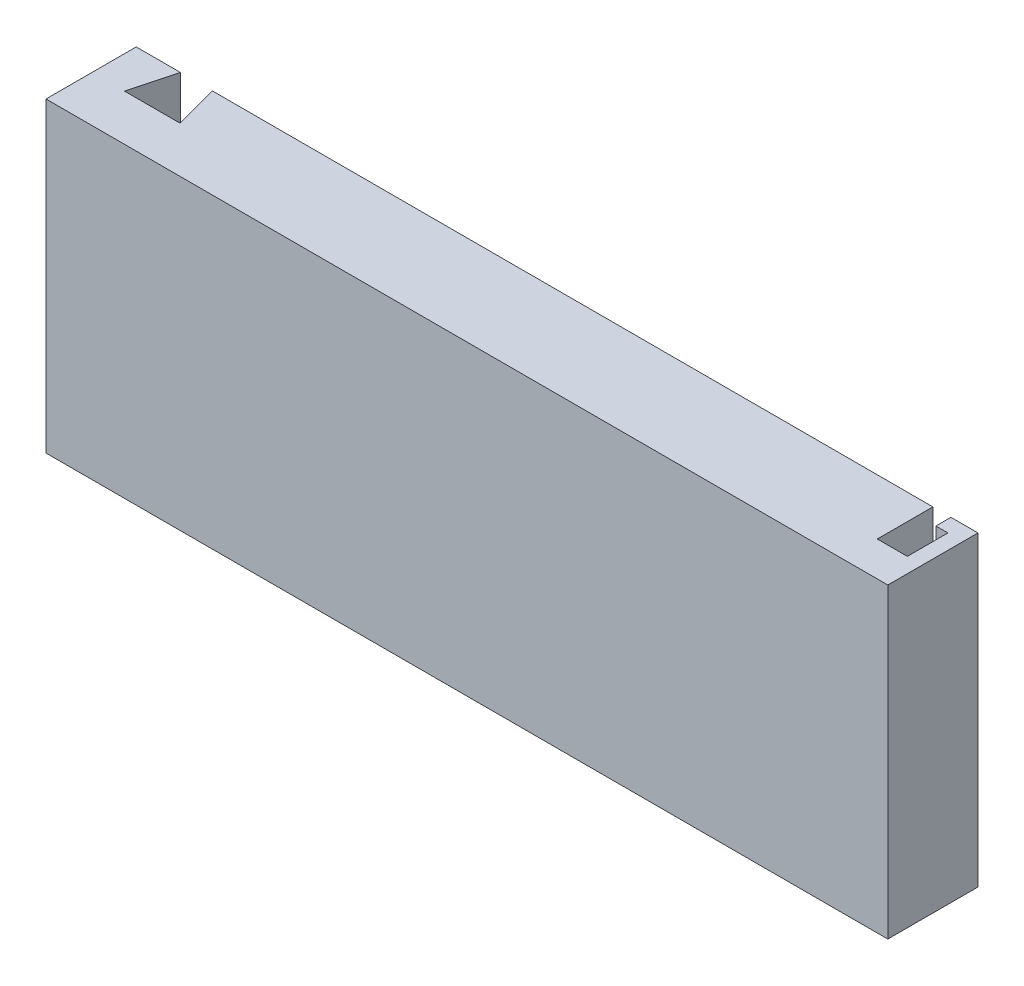
SolidWorks part; units mm, degrees
ref_plane "Front Plane" through (0, 0, 0) normal (0, 0, 1) x (1, 0, 0)
ref_plane "Top Plane" through (0, 0, 0) normal (0, 1, 0) x (1, 0, 0)
ref_plane "Right Plane" through (0, 0, 0) normal (1, 0, 0) x (0, 0, -1)
sketch "Sketch1" plane through (0, 0, 0) normal (0, 0, 1) x (1, 0, 0)
  line L1 (-60.9366, 28.6127) -> (79.0634, 28.6127)
  line L2 (-60.9366, 28.6127) -> (-60.9366, -22.3873)
  line L3 (-60.9366, -22.3873) -> (79.0634, -22.3873)
  line L4 (79.0634, 28.6127) -> (79.0634, -22.3873)
  dimension "D1" = 51
  dimension "D2" = 140
extrude "Boss-Extrude1" add sketch "Sketch1" along normal blind 15
sketch "Sketch2" plane through (0, 28.6127, 0) normal (0, 1, 0) x (1, 0, 0)
  line L0 (79.0634, 0) -> (74.5634, 0)
  line L6 (79.0634, 0) -> (-60.9366, 0) construction
  line L7 (74.5634, 0) -> (71.5634, 0)
  line L8 (71.5634, 0) -> (71.5634, -2.5)
  line L9 (71.5634, -2.5) -> (71.5634, -9.25)
  line L10 (71.5634, -9.25) -> (76.5634, -9.25)
  line L11 (74.5634, 0) -> (74.5634, -2.5)
  line L12 (74.5634, -2.5) -> (76.5634, -2.5)
  line L13 (76.5634, -2.5) -> (76.5634, -9.25)
  line M13 (79.0634, 0) -> (-60.9366, 0)
  dimension "D1" = 4.5
  dimension "D2" = 3
  dimension "D3" = 2.5
  dimension "D4" = 6.75
  dimension "D5" = 5
extrude "Cut-Extrude1" cut sketch "Sketch2" against normal through all contours L13 L12 L11 L8 L9 L10 M13
sketch "Sketch3" plane through (0, 28.6127, 0) normal (0, 1, 0) x (1, 0, 0)
  line L0 (-60.9366, 0) -> (-53.5866, 0)
  line L2 (71.5634, 0) -> (-60.9366, 0) construction
  line L3 (-53.5866, 0) -> (-55.5536, -7.341)
  line L4 (-55.5536, -7.341) -> (-46.3196, -7.341)
  line L5 (-46.3196, -7.341) -> (-48.2866, 0)
  dimension "D1" = 7.35
  dimension "D2" = 105
  dimension "D3" = 105
  dimension "D4" = 75
  dimension "D5" = 75
  dimension "D6" = 7.6
  dimension "D7" = 7.6
  dimension "D8" = 5.3
  dimension "D9" = 9.234
extrude "Cut-Extrude2" cut sketch "Sketch3" against normal blind 26 and the other way through all
